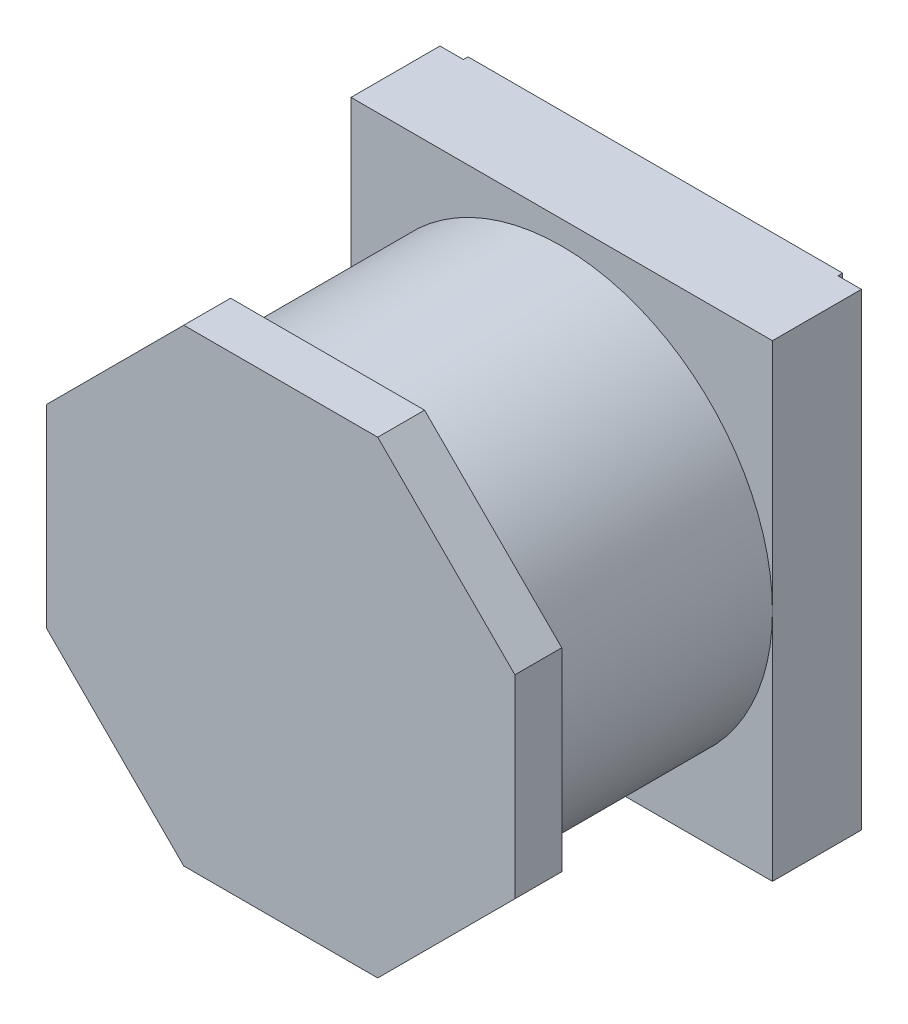
SolidWorks part; units mm, degrees
ref_plane "Front Plane" through (0, 0, 0) normal (0, 0, 1) x (1, 0, 0)
ref_plane "Top Plane" through (0, 0, 0) normal (0, 1, 0) x (1, 0, 0)
ref_plane "Right Plane" through (0, 0, 0) normal (1, 0, 0) x (0, 0, -1)
sketch "Sketch1" plane through (0, 0, 0) normal (0, 0, 1) x (1, 0, 0)
  line L1 (0, 0) -> (-4.5, 0)
  line L2 (0, 0) -> (0, 5)
  line L3 (0, 5) -> (-4.5, 5)
  line L4 (-4.5, 0) -> (-4.5, 5)
  dimension "D1" = 4.5
  dimension "D2" = 5
extrude "Boss-Extrude1" add sketch "Sketch1" along normal blind 1 contours L2 L3 L4 L1
sketch "Sketch2" plane through (0, 0, 1) normal (0, 0, 1) x (1, 0, 0)
  circle A0 centre (-2.25, 2.5) radius 2.25
extrude "Boss-Extrude2" add sketch "Sketch2" along normal blind 2.5
sketch "Sketch3" plane through (0, 0, 3.5) normal (0, 0, 1) x (1, 0, 0)
  line L1 (-1.2143, 5.0004) -> (-3.2857, 5.0004)
  line L2 (-3.2857, 5.0004) -> (-4.7504, 3.5357)
  line L3 (-4.7504, 3.5357) -> (-4.7504, 1.4643)
  line L4 (-4.7504, 1.4643) -> (-3.2857, -0.0004)
  line L5 (-3.2857, -0.0004) -> (-1.2143, -0.0004)
  line L6 (-1.2143, -0.0004) -> (0.2504, 1.4643)
  line L7 (0.2504, 1.4643) -> (0.2504, 3.5357)
  line L8 (0.2504, 3.5357) -> (-1.2143, 5.0004)
  circle A0 centre (-2.25, 2.5) radius 2.7064 construction
extrude "Boss-Extrude3" add sketch "Sketch3" along normal blind 0.5
sketch "Sketch5" plane through (0, 0, 0) normal (0, 0, -1) x (-1, 0, 0)
  line L0 (2.25, 5) -> (2.25, 0) construction
  line L1 (0, 5) -> (4.5, 5) construction
  line L2 (0, 0) -> (4.5, 0) construction
  line L3 (0.25, 5) -> (0, 5)
  line L4 (0, 5) -> (0, 0)
  line L5 (0.25, 5) -> (0.25, 3.75)
  line L6 (0.25, 3.75) -> (4.25, 3.75)
  line L7 (4.25, 5) -> (4.25, 3.75)
  line L9 (0.25, 0) -> (0.25, 1.25)
  line L10 (0.25, 1.25) -> (4.25, 1.25)
  line L11 (4.25, 0) -> (4.25, 1.25)
  line L12 (0, 0) -> (0.25, 0)
  line L13 (4.25, 0) -> (4.5, 0)
  line L14 (4.5, 0) -> (4.5, 5)
  line L15 (4.5, 5) -> (4.25, 5)
  point P14 (2.25, 3.75)
  point P15 (2.25, 1.25)
  dimension "D1" = 1.25
  dimension "D2" = 1.25
  dimension "D3" = 4
  dimension "D4" = 4
  dimension "D5" = 2.5
extrude "Cut-Extrude1" cut sketch "Sketch5" against normal blind 0.05
